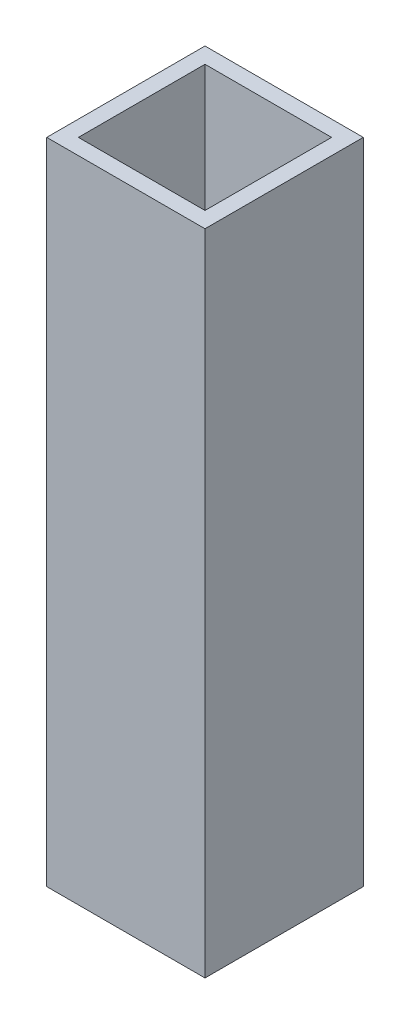
SolidWorks part; units mm, degrees
ref_plane "Front Plane" through (0, 0, 0) normal (0, 0, 1) x (1, 0, 0)
ref_plane "Top Plane" through (0, 0, 0) normal (0, 1, 0) x (1, 0, 0)
ref_plane "Right Plane" through (0, 0, 0) normal (1, 0, 0) x (0, 0, -1)
sketch "Sketch2" plane through (0, 0, 0) normal (0, 1, 0) x (1, 0, 0)
  line L0 (-25, 25) -> (25, 25)
  line L1 (-20, 20) -> (20, 20)
  line L2 (-20, 20) -> (-20, -20)
  line L3 (-20, -20) -> (20, -20)
  line L4 (20, 20) -> (20, -20)
  line L5 (-20, 20) -> (20, -20) construction
  line L6 (-20, -20) -> (20, 20) construction
  line L7 (25, 25) -> (25, -25)
  line L8 (-25, -25) -> (25, -25)
  line L9 (-25, 25) -> (-25, -25)
  point P0 (0, 0)
  dimension "D1" = 40
  dimension "D2" = 40
  dimension "D3" = 5
extrude "Boss-Extrude1" add sketch "Sketch2" along normal blind 205
